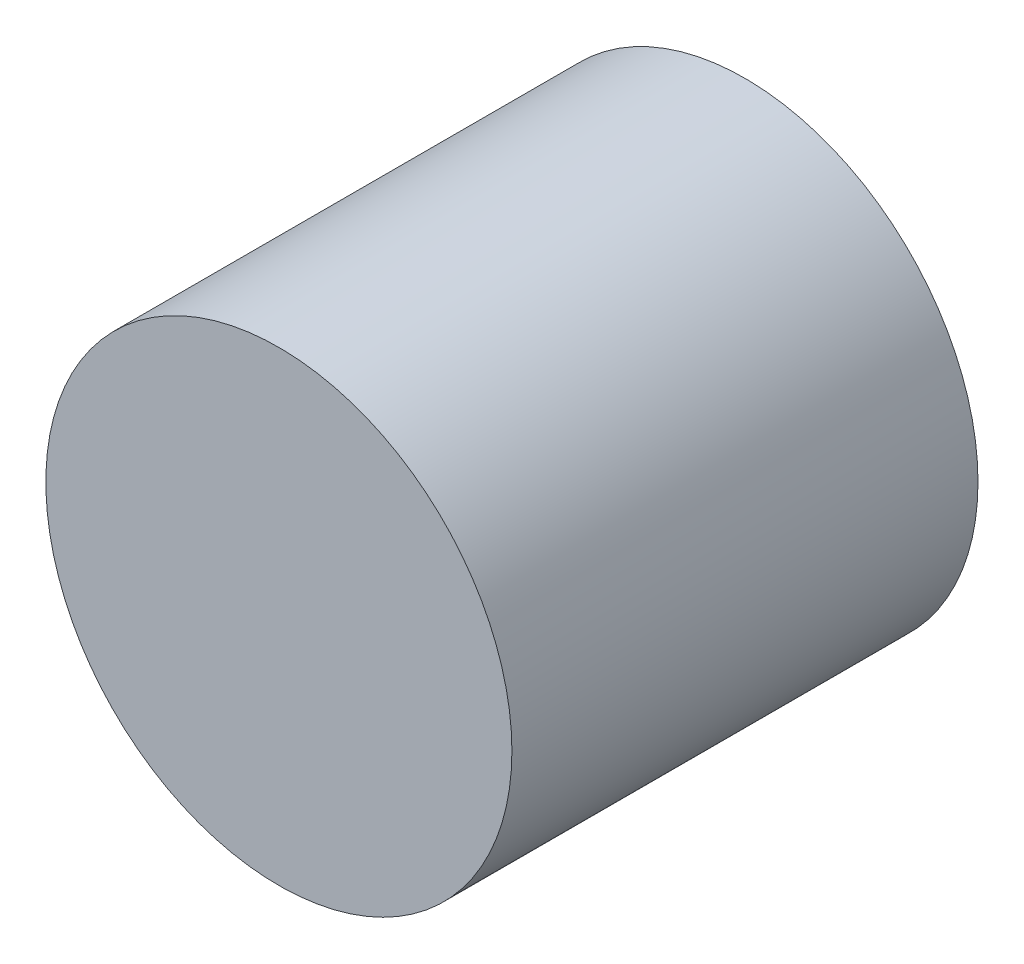
SolidWorks part; units mm, degrees
ref_plane "Front Plane" through (0, 0, 0) normal (0, 0, 1) x (1, 0, 0)
ref_plane "Top Plane" through (0, 0, 0) normal (0, 1, 0) x (1, 0, 0)
ref_plane "Right Plane" through (0, 0, 0) normal (1, 0, 0) x (0, 0, -1)
sketch "Sketch1" plane through (0, 0, 0) normal (0, 0, 1) x (1, 0, 0)
  circle A0 centre (0, 0) radius 25
  dimension "D1" = 50
extrude "Boss-Extrude1" add sketch "Sketch1" against normal blind 50
